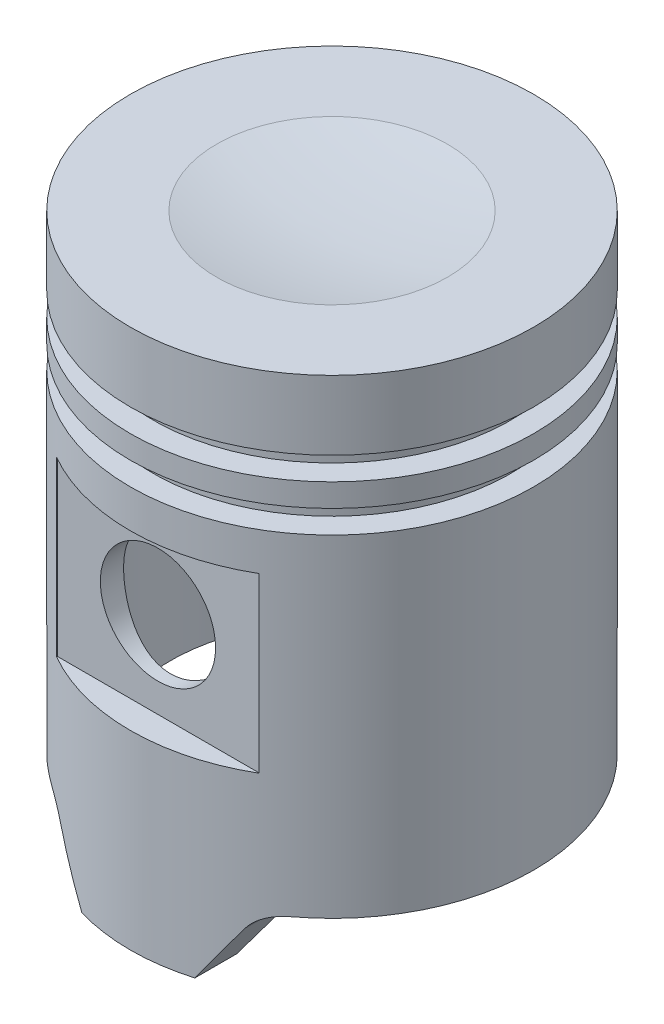
SolidWorks part; units mm, degrees
ref_plane "Front Plane" through (0, 0, 0) normal (0, 0, 1) x (1, 0, 0)
ref_plane "Top Plane" through (0, 0, 0) normal (0, 1, 0) x (1, 0, 0)
ref_plane "Right Plane" through (0, 0, 0) normal (1, 0, 0) x (0, 0, -1)
sketch "Sketch1" plane through (0, 0, 0) normal (0, 0, 1) x (1, 0, 0)
  line L0 (0, 0) -> (0, 58.166)
  line L1 (12.7127, 59.436) -> (22.225, 59.436)
  line L2 (22.225, 59.436) -> (22.225, 51.816)
  line L3 (22.225, 51.816) -> (19.685, 51.816)
  line L4 (19.685, 51.816) -> (19.685, 49.276)
  line L5 (19.685, 49.276) -> (22.225, 49.276)
  line L6 (22.225, 49.276) -> (22.225, 46.736)
  line L7 (22.225, 46.736) -> (19.685, 46.736)
  line L8 (19.685, 46.736) -> (19.685, 44.196)
  line L9 (19.685, 44.196) -> (22.225, 44.196)
  line L10 (22.225, 44.196) -> (22.225, 0)
  line L11 (22.225, 0) -> (0, 0)
  arc A0 (0, 58.166) -> (12.7127, 59.436) centre (0, 122.428) ccw
  point P15 (0, 0)
  point P16 (0, 0)
  point P17 (0, 0)
  dimension "D12" = 128.524
  dimension "D2" = 22.225
  dimension "D3" = 7.62
  dimension "D4" = 2.54
  dimension "D5" = 2.54
  dimension "D6" = 2.54
  dimension "D7" = 2.54
  dimension "D8" = 2.54
  dimension "D9" = 2.54
  dimension "D10" = 2.54
  dimension "D11" = 44.196
  dimension "D13" = 122.428
revolve "Revolve1" add sketch "Sketch1" angle 360 about L0
sketch "Sketch2" plane through (0, 0, 0) normal (0, -1, 0) x (1, 0, 0)
  circle A0 centre (0, 0) radius 17.78
  dimension "D1" = 35.56
extrude "Cut-Extrude1" cut sketch "Sketch2" against normal blind 51.816
sketch "Sketch3" plane through (0, 0, 0) normal (0, 0, 1) x (1, 0, 0)
  circle A0 centre (0, 30.48) radius 6.35
  point P2 (0, 0)
  dimension "D2" = 12.7
  dimension "D1" = 30.48
extrude "Cut-Extrude2" cut sketch "Sketch3" against normal through all both and the other way through all
sketch "Sketch4" plane through (0, 0, 0) normal (0, 0, 1) x (1, 0, 0)
  line L0 (-6.35, 30.48) -> (6.35, 30.48) construction
  line L1 (0, 36.83) -> (0, 24.13) construction
  line L3 (-11.049, 40.005) -> (11.176, 40.005)
  line L4 (-11.049, 40.005) -> (-11.049, 20.955)
  line L5 (-11.049, 20.955) -> (11.176, 20.955)
  line L6 (11.176, 40.005) -> (11.176, 20.955)
  circle A0 centre (0, 30.48) radius 6.35 construction
  circle A1 centre (0, 30.48) radius 6.35 construction
  point P13 (0, 30.48)
  dimension "D1" = 22.225
  dimension "D2" = 19.05
  dimension "D3" = 9.525
  dimension "D4" = 11.176
extrude "Cut-Extrude3" cut sketch "Sketch4" along normal through all from offset 19.177
mirror "Mirror1" about plane through (0, 0, 0) normal (0, 0, 1) of "Cut-Extrude3"
sketch "Sketch5" plane through (0, 0, 0) normal (0, 0, 1) x (1, 0, 0)
  line L0 (22.225, 0) -> (22.225, 7.62)
  line L1 (-22.225, 0) -> (22.225, 0) construction
  line L2 (22.225, 0) -> (22.225, 44.196) construction
  line L3 (22.225, 7.62) -> (13.3435, 7.62)
  line L4 (10.1738, 5.924) -> (6.223, 0)
  line L5 (6.223, 0) -> (22.225, 0)
  arc A0 (13.3435, 7.62) -> (10.1738, 5.924) centre (13.3435, 3.81) ccw
  dimension "D4" = 3.81
  dimension "D1" = 16.002
  dimension "D2" = 7.62
  dimension "D3" = 56.3
extrude "Cut-Extrude4" cut sketch "Sketch5" against normal through all both and the other way through all
mirror "Mirror2" about plane through (0, 0, 0) normal (1, 0, 0) of "Cut-Extrude4"
